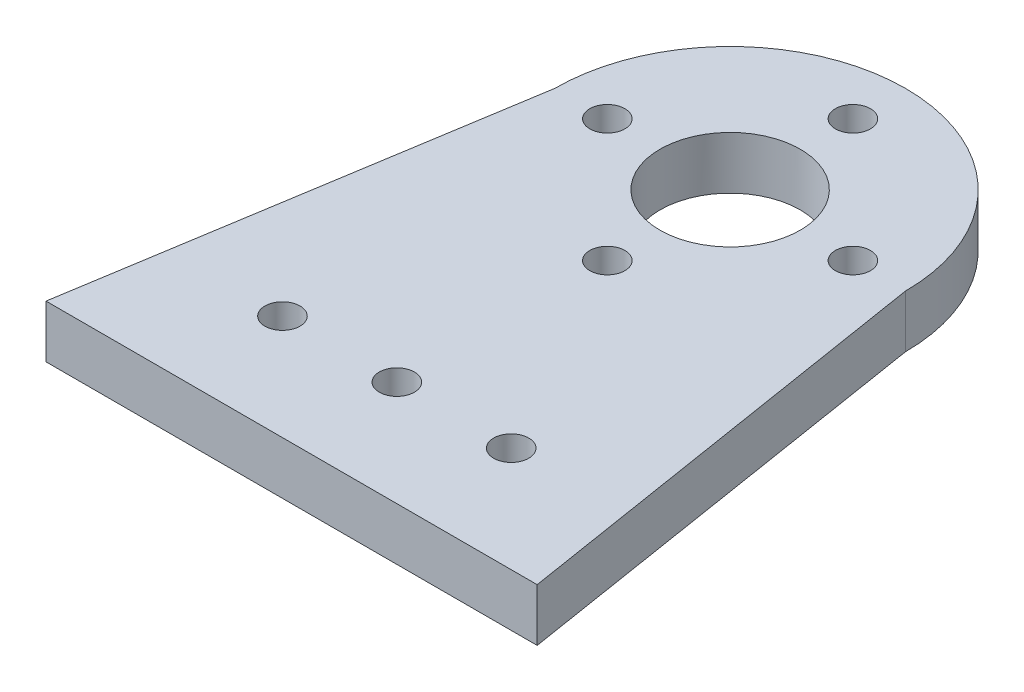
SolidWorks part; units mm, degrees
ref_plane "Front Plane" through (0, 0, 0) normal (0, 0, 1) x (1, 0, 0)
ref_plane "Top Plane" through (0, 0, 0) normal (0, 1, 0) x (1, 0, 0)
ref_plane "Right Plane" through (0, 0, 0) normal (1, 0, 0) x (0, 0, -1)
sketch "Sketch1" plane through (0, 0, 0) normal (0, 1, 0) x (1, 0, 0)
  line L0 (-10, 0) -> (-14, -25)
  line L1 (10, 0) -> (14, -25)
  line L2 (0, 17.2103) -> (0, -39.4896) construction
  line L3 (-14, -25) -> (14, -25)
  arc A0 (-10, 0) -> (10, 0) centre (0, 0) cw
  dimension "D1" = 10
  dimension "D2" = 25
  dimension "D3" = 14
extrude "Boss-Extrude1" add sketch "Sketch1" along normal blind 3
sketch "Sketch2" plane through (0, 3, 0) normal (0, 1, 0) x (1, 0, 0)
  line L0 (-21.4034, 0) -> (30.5216, 0) construction
  circle A0 centre (0, 0) radius 4
  dimension "D1" = 8
extrude "Cut-Extrude1" cut sketch "Sketch2" against normal blind 13
sketch "Sketch3" plane through (0, 3, 0) normal (0, 1, 0) x (1, 0, 0)
  line L0 (0, 14.8087) -> (0, -39.0944) construction
  line L1 (-14, -25) -> (14, -25) construction
  line L2 (-10, 0) -> (0, 0) construction
  line L3 (-13.04, -19) -> (0, -19) construction
  line L4 (-10, 0) -> (-14, -25) construction
  line L5 (14, -25) -> (10, 0) construction
  circle A0 centre (-6.52, -19) radius 1
  circle A1 centre (6.52, -19) radius 1
  circle A2 centre (0, -19) radius 1
  point P3 (-6.52, -19)
  point P11 (-13.04, -19)
  point P12 (13.0353, -18.9708)
  point P18 (0, -19)
  dimension "D3" = 2
  dimension "D2" = 2
  dimension "D1" = 6
extrude "Cut-Extrude2" cut sketch "Sketch3" against normal blind 13
sketch "Sketch4" plane through (0, 3, 0) normal (0, 1, 0) x (1, 0, 0)
  line L0 (0, 11.5358) -> (0, -14.2328) construction
  circle A0 centre (0, -7) radius 1
  circle A1 centre (-7, 0) radius 1
  circle A2 centre (0, 7) radius 1
  circle A3 centre (7, 0) radius 1
  point P0 (0, -7)
  point P15 (0, 0)
  dimension "D2" = 2
  dimension "D1" = 7
  dimension "D3" = 4
extrude "Cut-Extrude3" cut sketch "Sketch4" against normal up to vertex (3 mm away) up to point (0, 0, 0)
